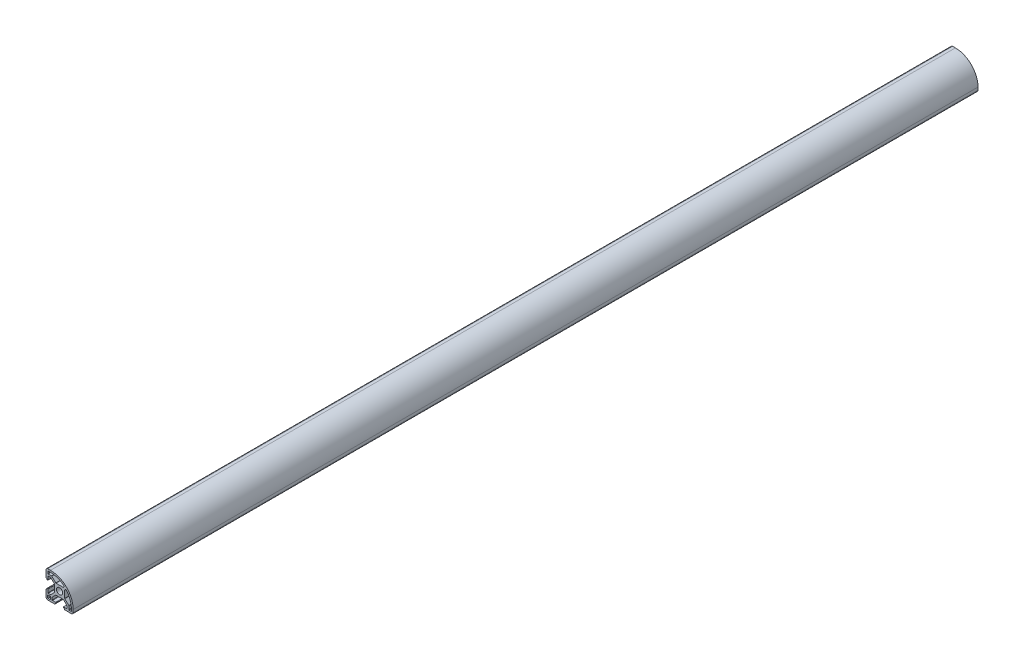
SolidWorks part; units mm, degrees
material "6063 T5"
ref_plane "Спереди" through (0, 0, 0) normal (0, 0, 1) x (1, 0, 0)
ref_plane "Сверху" through (0, 0, 0) normal (0, 1, 0) x (1, 0, 0)
ref_plane "Справа" through (0, 0, 0) normal (1, 0, 0) x (0, 0, -1)
sketch "Эскиз1" plane through (0, 0, 0) normal (0, 0, 1) x (1, 0, 0)
  line L0 (-15.0102, 15.2893) -> (14.9898, 15.2893) construction
  line L1 (-15, -8.25) -> (-15, -13)
  line L2 (-12.65, -9.85) -> (-10.35, -9.85)
  line L3 (-13.15, -10.35) -> (-13.15, -12.65)
  line L4 (-12.65, -13.15) -> (-10.35, -13.15)
  line L5 (-9.85, -10.35) -> (-9.85, -12.65)
  line L6 (-13, -15) -> (-8.25, -15)
  line L7 (-14.9949, 16.3613) -> (15.0051, 16.3613) construction
  line L12 (-15, 8.25) -> (-15, 13)
  line L13 (-13, 15) -> (-10, 15)
  line L18 (15, -10) -> (15, -13)
  line L19 (13, -15) -> (8.25, -15)
  line L24 (0, 0) -> (12.4128, 12.4128) construction
  line L25 (-13, 12.5) -> (-13, 10.75)
  line L26 (-12.5, 10.25) -> (-8.8958, 10.25)
  line L27 (-8.5423, 10.1036) -> (-4.2852, 5.8464)
  line L28 (-3.9316, 5.7) -> (3.8542, 5.7)
  line L29 (4.2077, 5.8464) -> (5.0472, 6.686)
  line L30 (-12.5, 13) -> (-10, 13)
  line L31 (13, -12.5) -> (13, -10)
  line L32 (12.5, -13) -> (10.75, -13)
  line L33 (10.25, -12.5) -> (10.25, -8.8958)
  line L34 (10.1036, -8.5423) -> (5.8464, -4.2852)
  line L35 (5.7, -3.9316) -> (5.7, 3.8542)
  line L36 (5.8464, 4.2077) -> (6.686, 5.0472)
  circle A0 centre (0, 0) radius 3.4
  arc A1 (-10.35, -13.15) -> (-9.85, -12.65) centre (-10.35, -12.65) ccw
  arc A2 (-13.15, -12.65) -> (-12.65, -13.15) centre (-12.65, -12.65) ccw
  arc A3 (-10.35, -9.85) -> (-9.85, -10.35) centre (-10.35, -10.35) cw
  arc A4 (-12.65, -9.85) -> (-13.15, -10.35) centre (-12.65, -10.35) ccw
  arc A5 (-15, -13) -> (-13, -15) centre (-13, -13) ccw
  arc A10 (-10, 15) -> (15, -10) centre (-10, -10) cw
  arc A15 (15, -13) -> (13, -15) centre (13, -13) cw
  arc A20 (-15, 13) -> (-13, 15) centre (-13, 13) cw
  arc A21 (-10, 13) -> (5.0202, 7.4182) centre (-10, -10) cw
  arc A22 (5.0472, 6.686) -> (5.0202, 7.4182) centre (4.6937, 7.0395) ccw
  arc A23 (3.8542, 5.7) -> (4.2077, 5.8464) centre (3.8542, 6.2) ccw
  arc A24 (-4.2852, 5.8464) -> (-3.9316, 5.7) centre (-3.9316, 6.2) ccw
  arc A25 (-8.8958, 10.25) -> (-8.5423, 10.1036) centre (-8.8958, 9.75) cw
  arc A26 (-13, 10.75) -> (-12.5, 10.25) centre (-12.5, 10.75) ccw
  arc A27 (-13, 12.5) -> (-12.5, 13) centre (-12.5, 12.5) cw
  arc A28 (12.5, -13) -> (13, -12.5) centre (12.5, -12.5) ccw
  arc A29 (10.75, -13) -> (10.25, -12.5) centre (10.75, -12.5) cw
  arc A30 (10.25, -8.8958) -> (10.1036, -8.5423) centre (9.75, -8.8958) ccw
  arc A31 (5.8464, -4.2852) -> (5.7, -3.9316) centre (6.2, -3.9316) cw
  arc A32 (5.7, 3.8542) -> (5.8464, 4.2077) centre (6.2, 3.8542) cw
  arc A33 (6.686, 5.0472) -> (7.4182, 5.0202) centre (7.0395, 4.6937) cw
  arc A34 (13, -10) -> (7.4182, 5.0202) centre (-10, -10) ccw
  point P5 (0, 0)
  point P16 (-13.15, -13.15)
  point P21 (-13.15, -9.85)
  point P52 (4.0613, 5.7)
  point P55 (-4.1387, 5.7)
  line B0 (-8.25, -15) -> (-5.5, -15)
  line B1 (-5.2, -14.7) -> (-5.2, -14)
  line B2 (-5.2, -14) -> (-4.4, -14)
  line B3 (-4.1, -13.7) -> (-4.1, -13.1)
  line B4 (-4.4, -12.8) -> (-7.95, -12.8)
  line B5 (-8.25, -12.5) -> (-8.25, -9.8)
  line B6 (-8.25, -9.8) -> (-4.25, -5.8)
  line B7 (0, -5.8) -> (0, -15) construction
  line B8 (4.25, -5.8) -> (-4.25, -5.8)
  line B9 (8.25, -9.8) -> (4.25, -5.8)
  line B10 (8.25, -12.5) -> (8.25, -9.8)
  line B11 (4.4, -12.8) -> (7.95, -12.8)
  line B12 (4.1, -13.7) -> (4.1, -13.1)
  line B13 (5.2, -14) -> (4.4, -14)
  line B14 (5.2, -14.7) -> (5.2, -14)
  line B15 (8.25, -15) -> (5.5, -15)
  arc B16 (-7.95, -12.8) -> (-8.25, -12.5) centre (-7.95, -12.5) cw
  arc B17 (-4.1, -13.1) -> (-4.4, -12.8) centre (-4.4, -13.1) ccw
  arc B18 (-4.4, -14) -> (-4.1, -13.7) centre (-4.4, -13.7) ccw
  arc B19 (-5.5, -15) -> (-5.2, -14.7) centre (-5.5, -14.7) ccw
  arc B20 (5.5, -15) -> (5.2, -14.7) centre (5.5, -14.7) cw
  arc B21 (4.4, -14) -> (4.1, -13.7) centre (4.4, -13.7) cw
  arc B22 (4.1, -13.1) -> (4.4, -12.8) centre (4.4, -13.1) cw
  arc B23 (7.95, -12.8) -> (8.25, -12.5) centre (7.95, -12.5) ccw
  line B24 (-15, 8.25) -> (-15, 5.5)
  line B25 (-14.7, 5.2) -> (-14, 5.2)
  line B26 (-14, 5.2) -> (-14, 4.4)
  line B27 (-13.7, 4.1) -> (-13.1, 4.1)
  line B28 (-12.8, 4.4) -> (-12.8, 7.95)
  line B29 (-12.5, 8.25) -> (-9.8, 8.25)
  line B30 (-9.8, 8.25) -> (-5.8, 4.25)
  line B31 (-5.8, 0) -> (-15, 0) construction
  line B32 (-5.8, -4.25) -> (-5.8, 4.25)
  line B33 (-9.8, -8.25) -> (-5.8, -4.25)
  line B34 (-12.5, -8.25) -> (-9.8, -8.25)
  line B35 (-12.8, -4.4) -> (-12.8, -7.95)
  line B36 (-13.7, -4.1) -> (-13.1, -4.1)
  line B37 (-14, -5.2) -> (-14, -4.4)
  line B38 (-14.7, -5.2) -> (-14, -5.2)
  line B39 (-15, -8.25) -> (-15, -5.5)
  arc B40 (-12.8, 7.95) -> (-12.5, 8.25) centre (-12.5, 7.95) cw
  arc B41 (-13.1, 4.1) -> (-12.8, 4.4) centre (-13.1, 4.4) ccw
  arc B42 (-14, 4.4) -> (-13.7, 4.1) centre (-13.7, 4.4) ccw
  arc B43 (-15, 5.5) -> (-14.7, 5.2) centre (-14.7, 5.5) ccw
  arc B44 (-15, -5.5) -> (-14.7, -5.2) centre (-14.7, -5.5) cw
  arc B45 (-14, -4.4) -> (-13.7, -4.1) centre (-13.7, -4.4) cw
  arc B46 (-13.1, -4.1) -> (-12.8, -4.4) centre (-13.1, -4.4) cw
  arc B47 (-12.8, -7.95) -> (-12.5, -8.25) centre (-12.5, -7.95) ccw
  dimension "D10" = 30
  dimension "D2" = 6.8
  dimension "D6" = 0.5
  dimension "D7" = 2
  dimension "D11" = 25
  dimension "D13" = 45
  dimension "D17" = 23
  dimension "D19" = 0.5
  dimension "D1" = 15
  dimension "D3" = 3.3
  dimension "D4" = 1.6
  dimension "D5" = 1.6
  dimension "D8" = 30
  dimension "D9" = 30
  dimension "D12" = 5
  dimension "D14" = 5.7
  dimension "D15" = 2.2
  dimension "D16" = 2
  dimension "D18" = 8.2
  dimension "D20" = 2
  dimension "D21" = 2
sketch_block_instance "Блок1-2"
sketch_block "Блок1" parameters "D7"=0.3, "D10"=0.3, "D1"=16.5, "D2"=2.2, "D3"=8.5, "D4"=9.2, "D5"=45, "D6"=10.4, "D8"=2.75, "D9"=0.4
sketch_block_instance "Блок1-4"
sketch_block_instance "Блок1-7"
sketch_block_instance "Блок1-8"
extrude "Бобышка-Вытянуть1" add sketch "Эскиз1" along normal blind 1000
